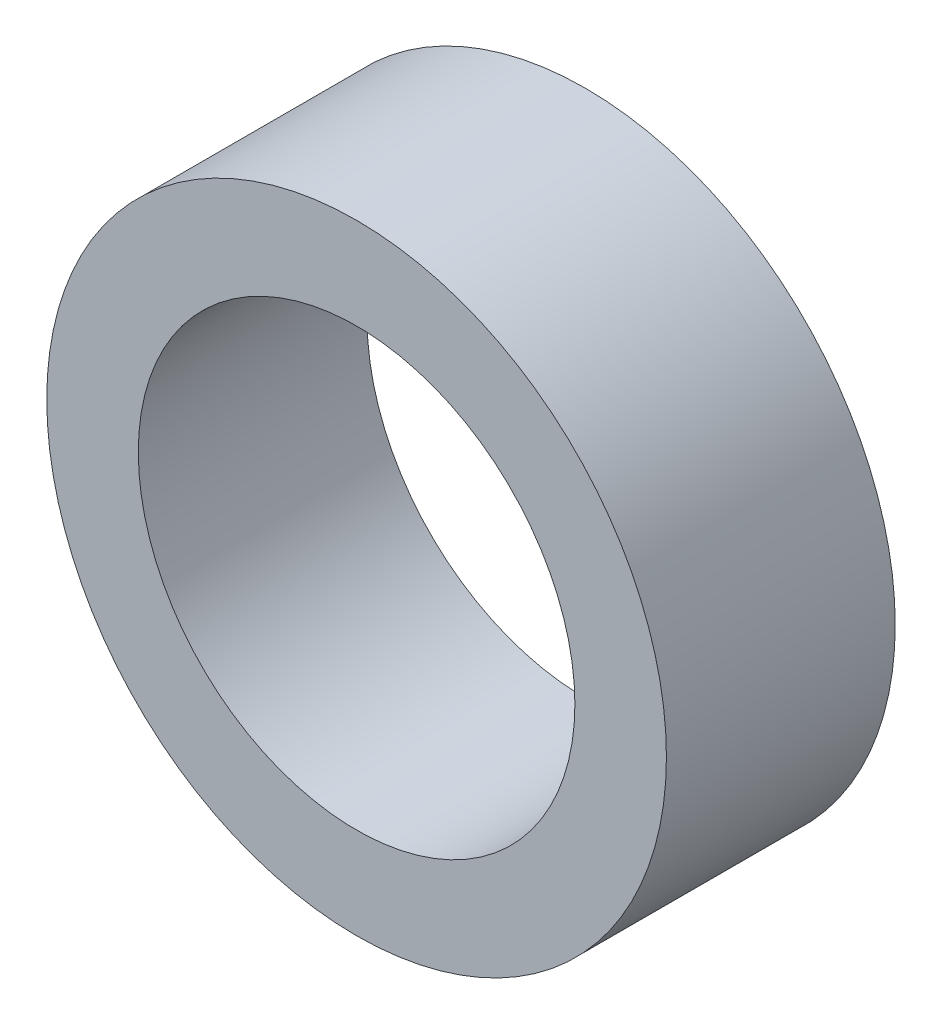
SolidWorks part; units mm, degrees
material "AISI Type 316L stainless steel"
ref_plane "Front Plane" through (0, 0, 0) normal (0, 0, 1) x (1, 0, 0)
ref_plane "Top Plane" through (0, 0, 0) normal (0, 1, 0) x (1, 0, 0)
ref_plane "Right Plane" through (0, 0, 0) normal (1, 0, 0) x (0, 0, -1)
sketch "Sketch1" plane through (0, 0, 0) normal (0, 0, 1) x (1, 0, 0)
  circle A0 centre (0, 0) radius 8.5985
  circle A1 centre (0, 0) radius 6.0585
  dimension "D1" = 17.197
  dimension "D2" = 2.54
extrude "Boss-Extrude1" add sketch "Sketch1" along normal blind 6.35 contours A1
